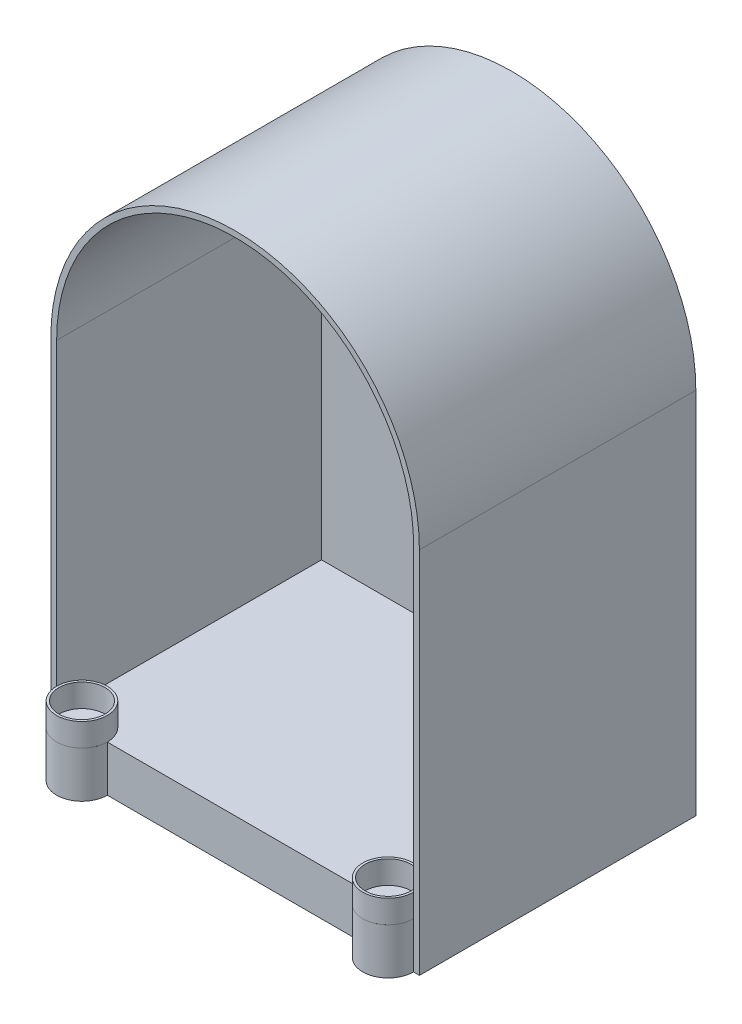
SolidWorks part; units mm, degrees
ref_plane "Front" through (0, 0, 0) normal (0, 0, 1) x (1, 0, 0)
ref_plane "Top" through (0, 0, 0) normal (0, 1, 0) x (1, 0, 0)
ref_plane "Right" through (0, 0, 0) normal (1, 0, 0) x (0, 0, -1)
sketch "Sketch1" plane through (0, 0, 0) normal (0, 0, 1) x (1, 0, 0)
  line L0 (0, 203.2) -> (0, 0)
  line L1 (0, 0) -> (203.2, 0)
  line L2 (203.2, 0) -> (203.2, 203.2)
  arc A0 (0, 203.2) -> (203.2, 203.2) centre (101.6, 203.2) cw
  dimension "D1" = 203.2
  dimension "D2" = 203.2
extrude "Boss-Extrude1" add sketch "Sketch1" along normal blind 152.4
sketch "Sketch2" plane through (0, 0, 152.4) normal (0, 0, 1) x (1, 0, 0)
  line L0 (3.175, 203.2) -> (3.175, 25.4)
  line L1 (3.175, 25.4) -> (200.025, 25.4)
  line L2 (200.025, 25.4) -> (200.025, 203.2)
  line L3 (0, 0) -> (203.2, 0) construction
  line L4 (0, 203.2) -> (0, 0) construction
  line L5 (203.2, 0) -> (203.2, 203.2) construction
  arc A0 (3.175, 203.2) -> (200.025, 203.2) centre (101.6, 203.2) cw
  dimension "D1" = 177.8
  dimension "D2" = 25.4
  dimension "D3" = 3.175
  dimension "D4" = 3.175
extrude "Cut-Extrude1" cut sketch "Sketch2" against normal blind 146.05
sketch "Sketch4" plane through (0, 0, 0) normal (0, 1, 0) x (1, 0, 0)
  line L0 (0, 0) -> (0, -50000) construction
  line L1 (3.175, -48.3945) -> (3.175, -199.3646) construction
  line L2 (31.115, -192.4972) -> (31.115, 49807.5028) construction
  line L3 (171.958, -152.4) -> (171.958, -50152.4) construction
  line L4 (0, -152.4) -> (50000, -152.4) construction
  line L6 (199.898, -152.4) -> (199.898, -50152.4) construction
  line L8 (3.175, -152.4) -> (31.115, -152.4)
  line L9 (171.958, -152.4) -> (199.898, -152.4)
  arc A1 (31.115, -152.4) -> (3.175, -152.4) centre (17.145, -152.4) cw
  arc A2 (171.958, -152.4) -> (199.898, -152.4) centre (185.928, -152.4) ccw
  point P11 (3.175, -152.4)
  point P12 (31.115, -152.4)
  point P16 (199.898, -152.4)
  point P17 (171.958, -152.4)
  dimension "D1" = 3.175
  dimension "D2" = 27.94
  dimension "D3" = 171.958
  dimension "D4" = 27.94
extrude "Boss-Extrude4" add sketch "Sketch4" along normal blind 25.4 contours A1 L8 | L9 A2
sketch "Sketch5" plane through (0, 25.4, 0) normal (0, 1, 0) x (1, 0, 0)
  circle A0 centre (17.145, -152.4) radius 13.97
  circle A1 centre (185.928, -152.4) radius 13.97
  point P7 (17.145, -152.4)
  point P8 (185.928, -152.4)
extrude "Boss-Extrude10" add sketch "Sketch5" along normal blind 12.7 separate body
sketch "Sketch6" plane through (0, 38.1, 0) normal (0, 1, 0) x (1, 0, 0)
  circle A0 centre (17.145, -152.4) radius 12.7
  circle A1 centre (185.928, -152.4) radius 12.7
extrude "Cut-Extrude2" cut sketch "Sketch6" against normal blind 12.7
